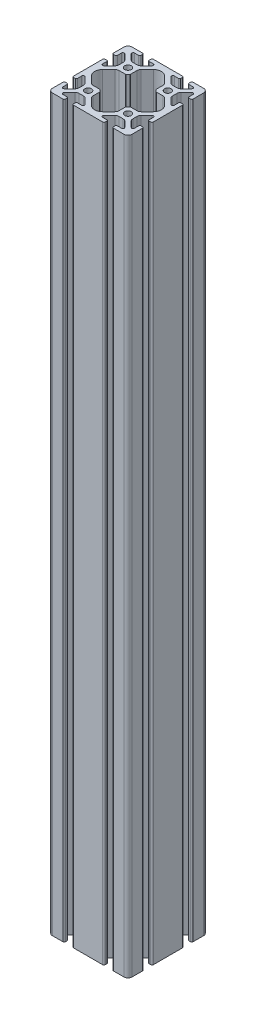
SolidWorks part; units mm, degrees
ref_plane "Piano frontale" through (0, 0, 0) normal (0, 0, 1) x (1, 0, 0)
ref_plane "Piano superiore" through (0, 0, 0) normal (0, 1, 0) x (1, 0, 0)
ref_plane "Piano destro" through (0, 0, 0) normal (1, 0, 0) x (0, 0, -1)
ref_plane "Piano1" through (0, -10, 0) normal (0, -1, 0) x (1, 0, 0)
sketch "Schizzo1" plane through (0, -10, 0) normal (0, -1, 0) x (1, 0, 0)
  line L0 (-4.2426, -23.3532) -> (-8.8713, -18.7245)
  line L1 (-9.75, -16.6032) -> (-9.75, -11.6703)
  line L2 (-9.8964, -11.3168) -> (-11.3168, -9.8964)
  line L3 (-11.6703, -9.75) -> (-16.6032, -9.75)
  line L4 (-18.7245, -8.8713) -> (-23.3532, -4.2426)
  line L5 (-23.3532, 4.2426) -> (-18.7245, 8.8713)
  line L6 (-16.6032, 9.75) -> (-11.6703, 9.75)
  line L7 (-11.3168, 9.8964) -> (-9.8964, 11.3168)
  line L8 (-9.75, 11.6703) -> (-9.75, 16.6032)
  line L9 (-8.8713, 18.7245) -> (-4.2426, 23.3532)
  line L10 (4.2426, 23.3532) -> (8.8713, 18.7245)
  line L11 (9.75, 16.6032) -> (9.75, 11.6703)
  line L12 (9.8964, 11.3168) -> (11.3168, 9.8964)
  line L13 (11.6703, 9.75) -> (16.6032, 9.75)
  line L14 (18.7245, 8.8713) -> (23.3532, 4.2426)
  line L15 (23.3532, -4.2426) -> (18.7245, -8.8713)
  line L16 (16.6032, -9.75) -> (11.6703, -9.75)
  line L17 (11.3168, -9.8964) -> (9.8964, -11.3168)
  line L18 (9.75, -11.6703) -> (9.75, -16.6032)
  line L19 (8.8713, -18.7245) -> (4.2426, -23.3532)
  line L20 (11.9, 27.8) -> (11.9, 29)
  line L21 (10.9, 30) -> (-10.9, 30)
  line L22 (-11.9, 29) -> (-11.9, 27.8)
  line L23 (-11.1, 27) -> (-7.8724, 27)
  line L24 (-7.1494, 25.2547) -> (-11.2755, 21.1287)
  line L25 (-13.3968, 20.25) -> (-16.6032, 20.25)
  line L26 (-18.7245, 21.1287) -> (-22.8506, 25.2547)
  line L27 (-22.1276, 27) -> (-18.9, 27)
  line L28 (-18.1, 27.8) -> (-18.1, 29)
  line L29 (-19.1, 30) -> (-27, 30)
  line L30 (-30, 27) -> (-30, 19.1)
  line L31 (-29, 18.1) -> (-27.8, 18.1)
  line L32 (-27, 18.9) -> (-27, 22.1276)
  line L33 (-25.2547, 22.8506) -> (-21.1287, 18.7245)
  line L34 (-20.25, 16.6032) -> (-20.25, 13.3968)
  line L35 (-21.1287, 11.2755) -> (-25.2547, 7.1494)
  line L36 (-27, 7.8724) -> (-27, 11.1)
  line L37 (-27.8, 11.9) -> (-29, 11.9)
  line L38 (-30, 10.9) -> (-30, -10.9)
  line L39 (-29, -11.9) -> (-27.8, -11.9)
  line L40 (-27, -11.1) -> (-27, -7.8724)
  line L41 (-25.2547, -7.1494) -> (-21.1287, -11.2755)
  line L42 (-20.25, -13.3968) -> (-20.25, -16.6032)
  line L43 (-21.1287, -18.7245) -> (-25.2547, -22.8506)
  line L44 (-27, -22.1276) -> (-27, -18.9)
  line L45 (-27.8, -18.1) -> (-29, -18.1)
  line L46 (-30, -19.1) -> (-30, -27)
  line L47 (-27, -30) -> (-19.1, -30)
  line L48 (-18.1, -29) -> (-18.1, -27.8)
  line L49 (-18.9, -27) -> (-22.1276, -27)
  line L50 (-22.8506, -25.2547) -> (-18.7245, -21.1287)
  line L51 (-16.6032, -20.25) -> (-13.3968, -20.25)
  line L52 (-11.2755, -21.1287) -> (-7.1494, -25.2547)
  line L53 (-7.8724, -27) -> (-11.1, -27)
  line L54 (-11.9, -27.8) -> (-11.9, -29)
  line L55 (-10.9, -30) -> (10.9, -30)
  line L56 (11.9, -29) -> (11.9, -27.8)
  line L57 (11.1, -27) -> (7.8724, -27)
  line L58 (7.1494, -25.2547) -> (11.2755, -21.1287)
  line L59 (13.3968, -20.25) -> (16.6032, -20.25)
  line L60 (18.7245, -21.1287) -> (22.8506, -25.2547)
  line L61 (22.1276, -27) -> (18.9, -27)
  line L62 (18.1, -27.8) -> (18.1, -29)
  line L63 (19.1, -30) -> (27, -30)
  line L64 (30, -27) -> (30, -19.1)
  line L65 (29, -18.1) -> (27.8, -18.1)
  line L66 (27, -18.9) -> (27, -22.1276)
  line L67 (25.2547, -22.8506) -> (21.1287, -18.7245)
  line L68 (20.25, -16.6032) -> (20.25, -13.3968)
  line L69 (21.1287, -11.2755) -> (25.2547, -7.1494)
  line L70 (27, -7.8724) -> (27, -11.1)
  line L71 (27.8, -11.9) -> (29, -11.9)
  line L72 (30, -10.9) -> (30, 10.9)
  line L73 (29, 11.9) -> (27.8, 11.9)
  line L74 (27, 11.1) -> (27, 7.8724)
  line L75 (25.2547, 7.1494) -> (21.1287, 11.2755)
  line L76 (20.25, 13.3968) -> (20.25, 16.6032)
  line L77 (21.1287, 18.7245) -> (25.2547, 22.8506)
  line L78 (27, 22.1276) -> (27, 18.9)
  line L79 (27.8, 18.1) -> (29, 18.1)
  line L80 (30, 19.1) -> (30, 27)
  line L81 (27, 30) -> (19.1, 30)
  line L82 (18.1, 29) -> (18.1, 27.8)
  line L83 (18.9, 27) -> (22.1276, 27)
  line L84 (22.8506, 25.2547) -> (18.7245, 21.1287)
  line L85 (16.6032, 20.25) -> (13.3968, 20.25)
  line L86 (11.2755, 21.1287) -> (7.1494, 25.2547)
  line L87 (7.8724, 27) -> (11.1, 27)
  circle A0 centre (-15, -15) radius 2.5
  circle A1 centre (15, -15) radius 2.5
  circle A2 centre (15, 15) radius 2.5
  circle A3 centre (-15, 15) radius 2.5
  arc A4 (-8.8713, -18.7245) -> (-9.75, -16.6032) centre (-6.75, -16.6032) cw
  arc A5 (-9.75, -11.6703) -> (-9.8964, -11.3168) centre (-10.25, -11.6703) ccw
  arc A6 (-11.3168, -9.8964) -> (-11.6703, -9.75) centre (-11.6703, -10.25) ccw
  arc A7 (-16.6032, -9.75) -> (-18.7245, -8.8713) centre (-16.6032, -6.75) cw
  arc A8 (-23.3532, -4.2426) -> (-23.3532, 4.2426) centre (-19.1106, 0) cw
  arc A9 (-18.7245, 8.8713) -> (-16.6032, 9.75) centre (-16.6032, 6.75) cw
  arc A10 (-11.6703, 9.75) -> (-11.3168, 9.8964) centre (-11.6703, 10.25) ccw
  arc A11 (-9.8964, 11.3168) -> (-9.75, 11.6703) centre (-10.25, 11.6703) ccw
  arc A12 (-9.75, 16.6032) -> (-8.8713, 18.7245) centre (-6.75, 16.6032) cw
  arc A13 (-4.2426, 23.3532) -> (4.2426, 23.3532) centre (0, 19.1106) cw
  arc A14 (8.8713, 18.7245) -> (9.75, 16.6032) centre (6.75, 16.6032) cw
  arc A15 (9.75, 11.6703) -> (9.8964, 11.3168) centre (10.25, 11.6703) ccw
  arc A16 (11.3168, 9.8964) -> (11.6703, 9.75) centre (11.6703, 10.25) ccw
  arc A17 (16.6032, 9.75) -> (18.7245, 8.8713) centre (16.6032, 6.75) cw
  arc A18 (23.3532, 4.2426) -> (23.3532, -4.2426) centre (19.1106, 0) cw
  arc A19 (18.7245, -8.8713) -> (16.6032, -9.75) centre (16.6032, -6.75) cw
  arc A20 (11.6703, -9.75) -> (11.3168, -9.8964) centre (11.6703, -10.25) ccw
  arc A21 (9.8964, -11.3168) -> (9.75, -11.6703) centre (10.25, -11.6703) ccw
  arc A22 (9.75, -16.6032) -> (8.8713, -18.7245) centre (6.75, -16.6032) cw
  arc A23 (4.2426, -23.3532) -> (-4.2426, -23.3532) centre (0, -19.1106) cw
  arc A24 (11.1, 27) -> (11.9, 27.8) centre (11.1, 27.8) ccw
  arc A25 (11.9, 29) -> (10.9, 30) centre (10.9, 29) ccw
  arc A26 (-10.9, 30) -> (-11.9, 29) centre (-10.9, 29) ccw
  arc A27 (-11.9, 27.8) -> (-11.1, 27) centre (-11.1, 27.8) ccw
  arc A28 (-7.8724, 27) -> (-7.1494, 25.2547) centre (-7.8724, 25.9776) cw
  arc A29 (-11.2755, 21.1287) -> (-13.3968, 20.25) centre (-13.3968, 23.25) cw
  arc A30 (-16.6032, 20.25) -> (-18.7245, 21.1287) centre (-16.6032, 23.25) cw
  arc A31 (-22.8506, 25.2547) -> (-22.1276, 27) centre (-22.1276, 25.9776) cw
  arc A32 (-18.9, 27) -> (-18.1, 27.8) centre (-18.9, 27.8) ccw
  arc A33 (-18.1, 29) -> (-19.1, 30) centre (-19.1, 29) ccw
  arc A34 (-27, 30) -> (-30, 27) centre (-27, 27) ccw
  arc A35 (-30, 19.1) -> (-29, 18.1) centre (-29, 19.1) ccw
  arc A36 (-27.8, 18.1) -> (-27, 18.9) centre (-27.8, 18.9) ccw
  arc A37 (-27, 22.1276) -> (-25.2547, 22.8506) centre (-25.9776, 22.1276) cw
  arc A38 (-21.1287, 18.7245) -> (-20.25, 16.6032) centre (-23.25, 16.6032) cw
  arc A39 (-20.25, 13.3968) -> (-21.1287, 11.2755) centre (-23.25, 13.3968) cw
  arc A40 (-25.2547, 7.1494) -> (-27, 7.8724) centre (-25.9776, 7.8724) cw
  arc A41 (-27, 11.1) -> (-27.8, 11.9) centre (-27.8, 11.1) ccw
  arc A42 (-29, 11.9) -> (-30, 10.9) centre (-29, 10.9) ccw
  arc A43 (-30, -10.9) -> (-29, -11.9) centre (-29, -10.9) ccw
  arc A44 (-27.8, -11.9) -> (-27, -11.1) centre (-27.8, -11.1) ccw
  arc A45 (-27, -7.8724) -> (-25.2547, -7.1494) centre (-25.9776, -7.8724) cw
  arc A46 (-21.1287, -11.2755) -> (-20.25, -13.3968) centre (-23.25, -13.3968) cw
  arc A47 (-20.25, -16.6032) -> (-21.1287, -18.7245) centre (-23.25, -16.6032) cw
  arc A48 (-25.2547, -22.8506) -> (-27, -22.1276) centre (-25.9776, -22.1276) cw
  arc A49 (-27, -18.9) -> (-27.8, -18.1) centre (-27.8, -18.9) ccw
  arc A50 (-29, -18.1) -> (-30, -19.1) centre (-29, -19.1) ccw
  arc A51 (-30, -27) -> (-27, -30) centre (-27, -27) ccw
  arc A52 (-19.1, -30) -> (-18.1, -29) centre (-19.1, -29) ccw
  arc A53 (-18.1, -27.8) -> (-18.9, -27) centre (-18.9, -27.8) ccw
  arc A54 (-22.1276, -27) -> (-22.8506, -25.2547) centre (-22.1276, -25.9776) cw
  arc A55 (-18.7245, -21.1287) -> (-16.6032, -20.25) centre (-16.6032, -23.25) cw
  arc A56 (-13.3968, -20.25) -> (-11.2755, -21.1287) centre (-13.3968, -23.25) cw
  arc A57 (-7.1494, -25.2547) -> (-7.8724, -27) centre (-7.8724, -25.9776) cw
  arc A58 (-11.1, -27) -> (-11.9, -27.8) centre (-11.1, -27.8) ccw
  arc A59 (-11.9, -29) -> (-10.9, -30) centre (-10.9, -29) ccw
  arc A60 (10.9, -30) -> (11.9, -29) centre (10.9, -29) ccw
  arc A61 (11.9, -27.8) -> (11.1, -27) centre (11.1, -27.8) ccw
  arc A62 (7.8724, -27) -> (7.1494, -25.2547) centre (7.8724, -25.9776) cw
  arc A63 (11.2755, -21.1287) -> (13.3968, -20.25) centre (13.3968, -23.25) cw
  arc A64 (16.6032, -20.25) -> (18.7245, -21.1287) centre (16.6032, -23.25) cw
  arc A65 (22.8506, -25.2547) -> (22.1276, -27) centre (22.1276, -25.9776) cw
  arc A66 (18.9, -27) -> (18.1, -27.8) centre (18.9, -27.8) ccw
  arc A67 (18.1, -29) -> (19.1, -30) centre (19.1, -29) ccw
  arc A68 (27, -30) -> (30, -27) centre (27, -27) ccw
  arc A69 (30, -19.1) -> (29, -18.1) centre (29, -19.1) ccw
  arc A70 (27.8, -18.1) -> (27, -18.9) centre (27.8, -18.9) ccw
  arc A71 (27, -22.1276) -> (25.2547, -22.8506) centre (25.9776, -22.1276) cw
  arc A72 (21.1287, -18.7245) -> (20.25, -16.6032) centre (23.25, -16.6032) cw
  arc A73 (20.25, -13.3968) -> (21.1287, -11.2755) centre (23.25, -13.3968) cw
  arc A74 (25.2547, -7.1494) -> (27, -7.8724) centre (25.9776, -7.8724) cw
  arc A75 (27, -11.1) -> (27.8, -11.9) centre (27.8, -11.1) ccw
  arc A76 (29, -11.9) -> (30, -10.9) centre (29, -10.9) ccw
  arc A77 (30, 10.9) -> (29, 11.9) centre (29, 10.9) ccw
  arc A78 (27.8, 11.9) -> (27, 11.1) centre (27.8, 11.1) ccw
  arc A79 (27, 7.8724) -> (25.2547, 7.1494) centre (25.9776, 7.8724) cw
  arc A80 (21.1287, 11.2755) -> (20.25, 13.3968) centre (23.25, 13.3968) cw
  arc A81 (20.25, 16.6032) -> (21.1287, 18.7245) centre (23.25, 16.6032) cw
  arc A82 (25.2547, 22.8506) -> (27, 22.1276) centre (25.9776, 22.1276) cw
  arc A83 (27, 18.9) -> (27.8, 18.1) centre (27.8, 18.9) ccw
  arc A84 (29, 18.1) -> (30, 19.1) centre (29, 19.1) ccw
  arc A85 (30, 27) -> (27, 30) centre (27, 27) ccw
  arc A86 (19.1, 30) -> (18.1, 29) centre (19.1, 29) ccw
  arc A87 (18.1, 27.8) -> (18.9, 27) centre (18.9, 27.8) ccw
  arc A88 (22.1276, 27) -> (22.8506, 25.2547) centre (22.1276, 25.9776) cw
  arc A89 (18.7245, 21.1287) -> (16.6032, 20.25) centre (16.6032, 23.25) cw
  arc A90 (13.3968, 20.25) -> (11.2755, 21.1287) centre (13.3968, 23.25) cw
  arc A91 (7.1494, 25.2547) -> (7.8724, 27) centre (7.8724, 25.9776) cw
extrude "Estrusione-Estrusione1" add sketch "Schizzo1" against normal blind 550
